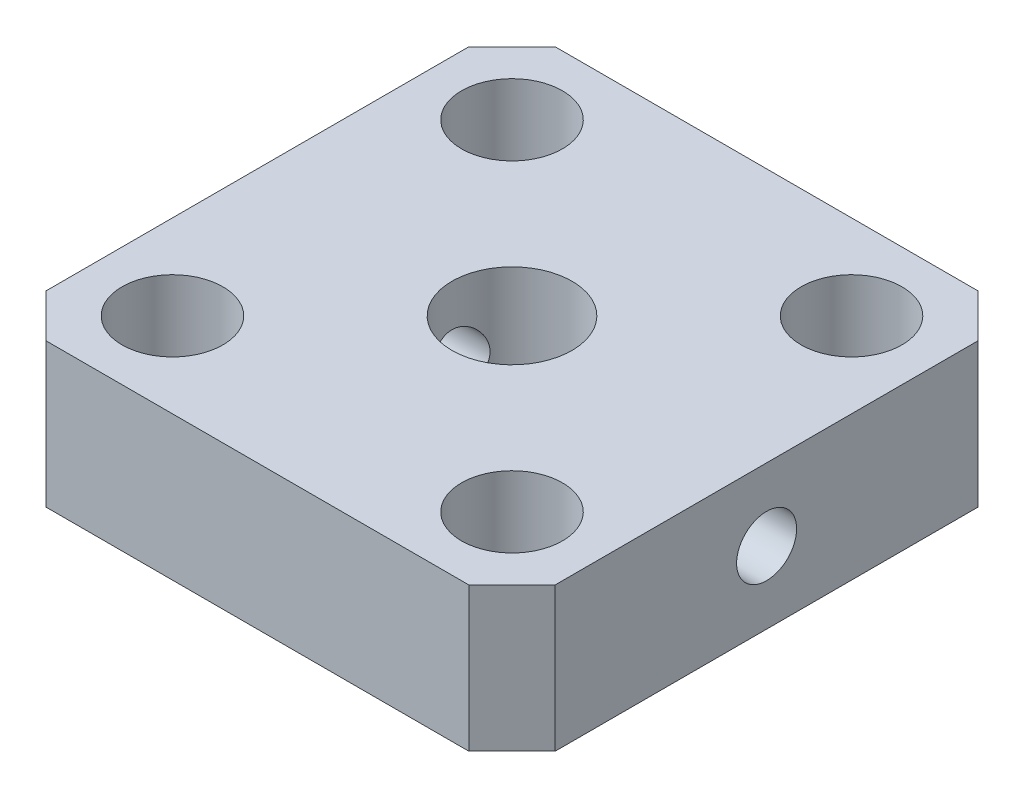
SolidWorks part; units mm, degrees
material "6061-T6 (SS)"
ref_plane "Front Plane" through (0, 0, 0) normal (0, 0, 1) x (1, 0, 0)
ref_plane "Top Plane" through (0, 0, 0) normal (0, 1, 0) x (1, 0, 0)
ref_plane "Right Plane" through (0, 0, 0) normal (1, 0, 0) x (0, 0, -1)
sketch "Sketch1" plane through (0, 0, 0) normal (0, 1, 0) x (1, 0, 0)
  line L1 (10.605, -10.605) -> (-10.605, -10.605)
  line L2 (10.605, -10.605) -> (10.605, 10.605)
  line L3 (10.605, 10.605) -> (-10.605, 10.605)
  line L4 (-10.605, -10.605) -> (-10.605, 10.605)
  line L5 (10.605, -10.605) -> (-10.605, 10.605) construction
  line L6 (10.605, 10.605) -> (-10.605, -10.605) construction
  circle A0 centre (0, 0) radius 2.5
  point P0 (0, 0)
  dimension "D2" = 5
  dimension "D1" = 21.21
extrude "Boss-Extrude1" add sketch "Sketch1" along normal blind 6
hole_wizard "M5x0.8 Tapped Hole1" positions "Sketch3" profile "Sketch2" tap size "M5x0.8" standard "ANSI Metric" end condition through all
sketch "Sketch3" plane through (0, 6, 0) normal (0, 1, 0) x (1, 0, 0)
  line L0 (-5.1965, 0) -> (0, 0) construction
  line L1 (0, 0) -> (0, 4.6768) construction
  line L3 (-7.0711, 7.0711) -> (0, 0) construction
  point P0 (-7.0711, 7.0711)
  point P11 (-7.0711, -7.0711)
  point P13 (7.0711, -7.0711)
  point P14 (7.0711, 7.0711)
  dimension "D1" = 20
  dimension "D2" = 45
sketch "Sketch2" plane through (-7.0711, 6, -7.0711) normal (1, 0, 0) x (0, 0, 1)
  line L0 (0, 0) -> (0, 6)
  line L1 (0, 6) -> (2.1, 6)
  line L2 (2.1, 6) -> (2.1, 0)
  line L5 (2.1, 0) -> (0, 0)
  line L11 (0, -6.35) -> (0, 107.95) construction
  dimension "Thread Major Dia." = 4.2
  dimension "Thru Tap Drill Depth" = 6
hole_wizard "M3x0.5 Tapped Hole1" positions "Sketch5" profile "Sketch4" tap size "M3x0.5" standard "ANSI Metric" end condition through all
sketch "Sketch5" plane through (10.605, 0, 0) normal (1, 0, 0) x (0, 0, -1)
  line L0 (0, 0) -> (0, 3) construction
  point P0 (0, 3)
  dimension "D1" = 3
sketch "Sketch4" plane through (10.605, 3, 0) normal (0, 1, 0) x (0, 0, -1)
  line L0 (0, 0) -> (0, 21.21)
  line L1 (0, 21.21) -> (1.25, 21.21)
  line L2 (1.25, 21.21) -> (1.25, 0)
  line L5 (1.25, 0) -> (0, 0)
  line L11 (0, -6.35) -> (0, 107.95) construction
  dimension "Thread Major Dia." = 2.5
  dimension "Thru Tap Drill Depth" = 21.21
chamfer "Chamfer1" distance 1.8 angle 45 4 edges at (10.605, 3, -10.605) (-10.605, 3, -10.605) (-10.605, 3, 10.605) (10.605, 3, 10.605)
